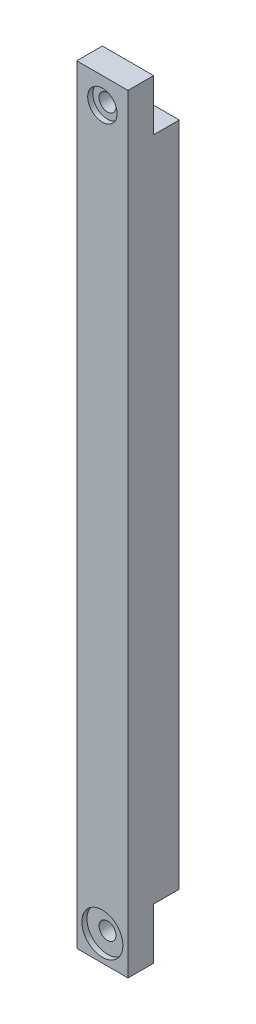
SolidWorks part; units mm, degrees
ref_plane "前视基准面" through (0, 0, 0) normal (0, 0, 1) x (1, 0, 0)
ref_plane "上视基准面" through (0, 0, 0) normal (0, 1, 0) x (1, 0, 0)
ref_plane "右视基准面" through (0, 0, 0) normal (1, 0, 0) x (0, 0, -1)
other "Configuration Table"
sketch "草图1" plane through (0, 0, 0) normal (0, 0, 1) x (1, 0, 0)
  line L1 (0, 0) -> (10, 0)
  line L2 (0, 0) -> (0, -150)
  line L3 (0, -150) -> (10, -150)
  line L4 (10, 0) -> (10, -150)
  line L5 (0, 0) -> (10, -150) construction
  line L6 (0, -150) -> (10, 0) construction
  point P4 (5, -75)
  dimension "D1" = 10
  dimension "D2" = 150
extrude "凸台-拉伸1" add sketch "草图1" along normal blind 10
sketch "草图3" plane through (0, 0, 0) normal (0, 0, -1) x (-1, 0, 0)
  line L0 (0, 0) -> (0, -150) construction
  line L1 (-10, 0) -> (0, 0)
  line L2 (-10, 0) -> (-10, -10)
  line L3 (-10, -10) -> (0, -10)
  line L4 (0, 0) -> (0, -10)
  line L5 (-10, 0) -> (0, -10) construction
  line L6 (-10, -10) -> (0, 0) construction
  line L8 (-10, -150) -> (0, -150)
  line L9 (-10, -150) -> (-10, -140)
  line L10 (-10, -140) -> (0, -140)
  line L11 (0, -150) -> (0, -140)
  line L12 (-10, -150) -> (0, -140) construction
  line L13 (-10, -140) -> (0, -150) construction
  point P4 (-5, -5)
  point P12 (-5, -145)
  dimension "D1" = 10
  dimension "D2" = 10
extrude "切除-拉伸1" cut sketch "草图3" against normal blind 5
sketch "草图7" plane through (0, 0, 10) normal (0, 0, 1) x (1, 0, 0)
  line L0 (10, -150) -> (10, 0) construction
  line L1 (0, 0) -> (10, 0) construction
  line L2 (0, 0) -> (0, -10) construction
  line L3 (0, -10) -> (10, -10) construction
  line L4 (10, 0) -> (10, -10) construction
  line L5 (0, 0) -> (10, -10) construction
  line L6 (0, -10) -> (10, 0) construction
  line L8 (0, -150) -> (10, -150) construction
  line L9 (0, -150) -> (0, -140) construction
  line L10 (0, -140) -> (10, -140) construction
  line L11 (10, -150) -> (10, -140) construction
  line L12 (0, -150) -> (10, -140) construction
  line L13 (0, -140) -> (10, -150) construction
  circle A0 centre (5, -5) radius 2.8681
  circle A1 centre (5, -145) radius 4
  point P4 (5, -5)
  point P12 (5, -145)
  dimension "D1" = 10
  dimension "D2" = 10
hole_wizard "M4 螺纹孔1" positions "草图8" profile "草图9" tap size "M4" standard "ISO" end condition through all
sketch "草图8" plane through (0, 0, 10) normal (0, 0, 1) x (1, 0, 0)
  point P0 (5, -5)
  point P3 (5, -145)
sketch "草图9" plane through (5, -5, 10) normal (1, 0, 0) x (0, -1, 0)
  line L0 (0, 0) -> (0, 10)
  line L1 (0, 10) -> (1.65, 10)
  line L2 (1.65, 10) -> (1.65, 0)
  line L5 (1.65, 0) -> (0, 0)
  line L11 (0, -6.35) -> (0, 107.95) construction
  dimension "通孔螺纹孔钻头直径" = 3.3
  dimension "通孔螺纹孔钻头深度" = 10
cosmetic thread "孔螺蚊线1" parameters "D2"=4
cosmetic thread "孔螺蚊线2" parameters "D2"=4
extrude "切除-拉伸2" cut sketch "草图7" against normal blind 1
